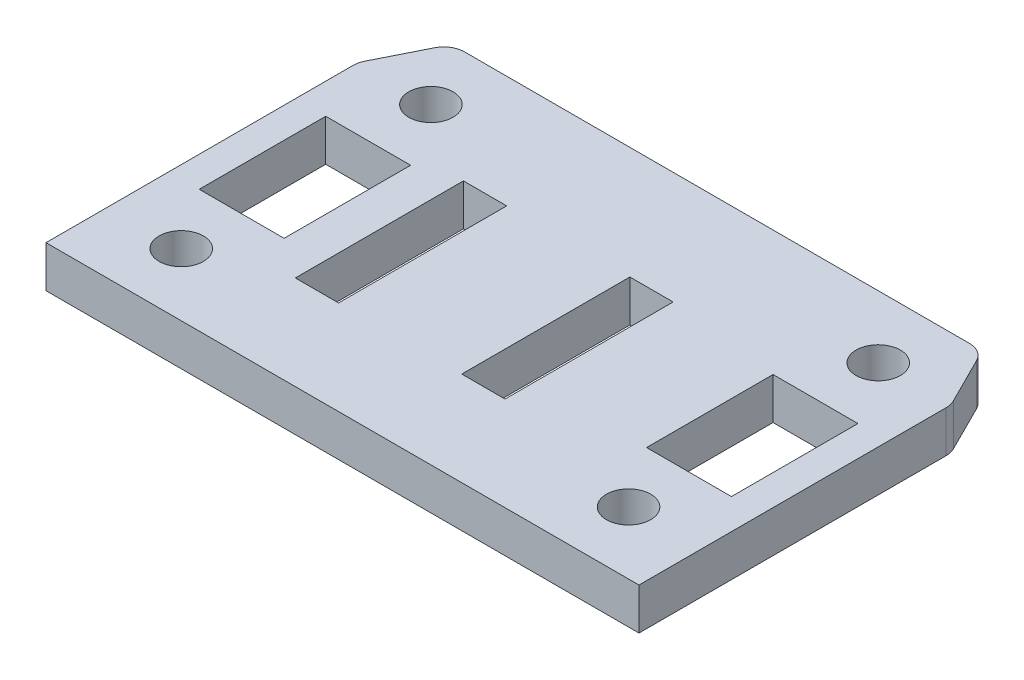
SolidWorks part; units mm, degrees
material "Plain Carbon Steel"
ref_plane "Front Plane" through (0, 0, 0) normal (0, 0, 1) x (1, 0, 0)
ref_plane "Top Plane" through (0, 0, 0) normal (0, 1, 0) x (1, 0, 0)
ref_plane "Right Plane" through (0, 0, 0) normal (1, 0, 0) x (0, 0, -1)
sketch "Sketch1" plane through (0, 0, 0) normal (0, 1, 0) x (1, 0, 0)
  line L0 (0, 28.575) -> (0, 0) construction
  line L1 (-40.4812, -28.575) -> (40.4812, -28.575)
  line L2 (-40.4812, -28.575) -> (-40.4812, 28.575)
  line L3 (-40.4812, 28.575) -> (40.4812, 28.575)
  line L4 (40.4812, -28.575) -> (40.4812, 28.575)
  line L5 (0, 0) -> (40.4812, 0) construction
  dimension "D1" = 40.4812
  dimension "D2" = 28.575
extrude "Boss-Extrude1" add sketch "Sketch1" along normal blind 6.35
sketch "Sketch2" plane through (0, 0, 0) normal (0, -1, 0) x (-1, 0, 0)
  line L0 (-3.8418, 11.4373) -> (-3.8418, -14.2167)
  line L1 (21.4312, -14.0897) -> (15.0812, -14.0897)
  line L2 (21.4312, -14.0897) -> (21.4312, 11.3103)
  line L3 (21.4312, 11.3103) -> (15.0812, 11.3103)
  line L4 (15.0812, -14.0897) -> (15.0812, 11.3103)
  line L5 (-3.9688, 11.3103) -> (-10.3188, 11.3103)
  line L6 (-3.9688, 11.3103) -> (-3.9688, -14.0897)
  line L7 (-3.9688, -14.0897) -> (-10.3188, -14.0897)
  line L8 (-10.3188, 11.3103) -> (-10.3188, -14.0897)
  line L9 (-3.8418, -14.2167) -> (-10.4458, -14.2167)
  line L10 (-10.4458, 11.4373) -> (-10.4458, -14.2167)
  line L11 (-3.8418, 11.4373) -> (-10.4458, 11.4373)
  line L12 (14.9542, -14.2167) -> (14.9542, 11.4373)
  line L13 (21.5582, 11.4373) -> (14.9542, 11.4373)
  line L14 (21.5582, -14.2167) -> (21.5582, 11.4373)
  line L15 (21.5582, -14.2167) -> (14.9542, -14.2167)
  dimension "D1" = 0.127
extrude "Cut-Extrude1" cut sketch "Sketch2" against normal through all
hole_wizard "1/4 Clearance Hole1" positions "Sketch4" profile "Sketch3" hole size "1/4" standard "ANSI Inch" end condition through all
sketch "Sketch4" plane through (0, 6.35, 0) normal (0, 1, 0) x (1, 0, 0)
  line L0 (-34.1312, 19.05) -> (-34.1312, -19.05) construction
  line L1 (-34.1312, -19.05) -> (34.1312, -19.05) construction
  line L2 (34.1312, -19.05) -> (34.1312, 19.05) construction
  line L3 (34.1312, 19.05) -> (-34.1312, 19.05) construction
  line L5 (-40.4812, 28.575) -> (-40.4812, -28.575) construction
  line L6 (40.4812, -28.575) -> (40.4812, 28.575) construction
  line L7 (-40.4812, -28.575) -> (40.4812, -28.575) construction
  line L8 (40.4812, 28.575) -> (-40.4812, 28.575) construction
  point P0 (-34.1312, 19.05)
  point P2 (-34.1312, -19.05)
  point P4 (34.1312, -19.05)
  point P6 (34.1312, 19.05)
  dimension "D1" = 6.35
  dimension "D2" = 6.35
  dimension "D3" = 9.525
  dimension "D4" = 9.525
sketch "Sketch3" plane through (-34.1312, 6.35, -19.05) normal (1, 0, 0) x (0, 0, 1)
  line L0 (0, 0) -> (0, 6.35)
  line L1 (0, 6.35) -> (3.3782, 6.35)
  line L2 (3.3782, 6.35) -> (3.3782, 0)
  line L5 (3.3782, 0) -> (0, 0)
  line L11 (0, -6.35) -> (0, 107.95) construction
  dimension "Thru Hole Dia." = 6.7564
  dimension "Thru Hole Depth" = 6.35
sketch "Sketch5" plane through (0, 6.35, 0) normal (0, 1, 0) x (1, 0, 0)
  line L0 (-45.2437, 19.05) -> (-40.4812, 28.575)
  line L1 (-40.4812, -28.575) -> (-45.2437, -28.575)
  line L2 (-40.4812, -28.575) -> (-40.4812, 19.05)
  line L3 (-40.4812, 19.05) -> (-45.2437, 19.05)
  line L4 (-45.2437, -28.575) -> (-45.2437, 19.05)
  line L5 (40.4812, -28.575) -> (45.2437, -28.575)
  line L6 (40.4812, -28.575) -> (40.4812, 19.05)
  line L7 (40.4812, 19.05) -> (45.2437, 19.05)
  line L8 (45.2437, -28.575) -> (45.2437, 19.05)
  line L9 (-40.4812, 28.575) -> (-40.4812, 19.05)
  line L10 (45.2437, 19.05) -> (40.4812, 28.575)
  line L11 (40.4812, 28.575) -> (40.4812, 19.05)
  line M13 (-40.4812, 28.575) -> (-40.4812, -28.575)
  line M15 (40.4812, -28.575) -> (40.4812, 28.575)
  dimension "D1" = 4.7625
  dimension "D2" = 47.625
extrude "Boss-Extrude3" add sketch "Sketch5" against normal up to surface (6.35 mm away) contours L5 L8 L7 M15 | L7 L10 M15 | L4 L1 L3 M13 | L3 L0 M13 up to face at (-34.1312, 0, -15.6718)
fillet "Fillet1" radius 3.175 4 edges at (-45.2437, 3.175, -19.05) (-40.4812, 3.175, -28.575) (40.4812, 3.175, -28.575) (45.2437, 3.175, -19.05)
sketch "Sketch6" plane through (0, 6.35, 0) normal (0, 1, 0) x (1, 0, 0)
  line L0 (-27.6542, -9.8289) -> (-27.6542, 9.4751)
  line L1 (-40.4812, -9.7019) -> (-27.7812, -9.7019)
  line L2 (-40.4812, -9.7019) -> (-40.4812, 9.3481)
  line L3 (-40.4812, 9.3481) -> (-27.7812, 9.3481)
  line L4 (-27.7812, -9.7019) -> (-27.7812, 9.3481)
  line L5 (27.7813, -9.7019) -> (40.4813, -9.7019)
  line L6 (27.7813, -9.7019) -> (27.7813, 9.3481)
  line L7 (27.7813, 9.3481) -> (40.4813, 9.3481)
  line L8 (40.4813, -9.7019) -> (40.4813, 9.3481)
  line L9 (-40.6082, 9.4751) -> (-27.6542, 9.4751)
  line L10 (-40.6082, -9.8289) -> (-40.6082, 9.4751)
  line L11 (-40.6082, -9.8289) -> (-27.6542, -9.8289)
  line L12 (40.6083, -9.8289) -> (40.6083, 9.4751)
  line L13 (27.6543, 9.4751) -> (40.6083, 9.4751)
  line L14 (27.6543, -9.8289) -> (27.6543, 9.4751)
  line L15 (27.6543, -9.8289) -> (40.6083, -9.8289)
  dimension "D1" = 19.05
  dimension "D2" = 0.127
extrude "Cut-Extrude2" cut sketch "Sketch6" against normal through all
